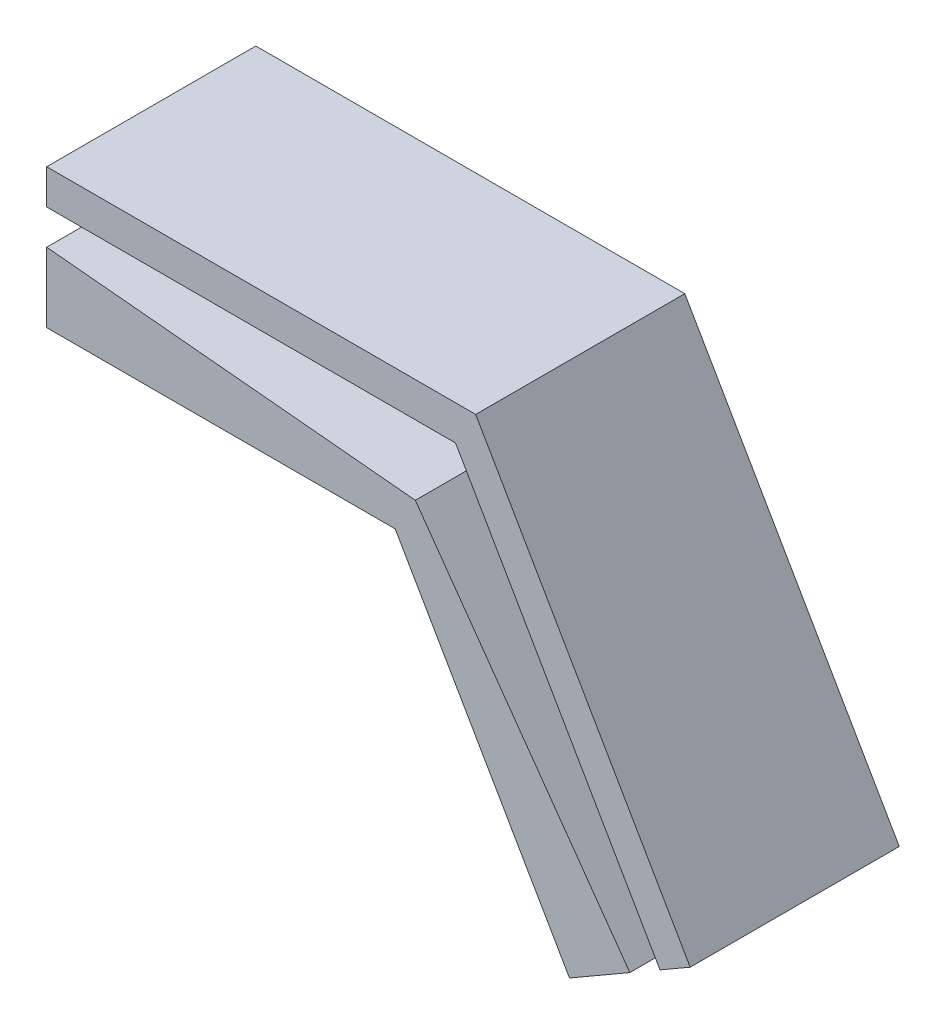
SolidWorks part; units mm, degrees
ref_plane "Alzado" through (0, 0, 0) normal (0, 0, 1) x (1, 0, 0)
ref_plane "Planta" through (0, 0, 0) normal (0, 1, 0) x (1, 0, 0)
ref_plane "Vista lateral" through (0, 0, 0) normal (1, 0, 0) x (0, 0, -1)
sketch "Croquis1" plane through (0, 0, 0) normal (0, 0, 1) x (1, 0, 0)
  line L0 (-111.6684, 35.9239) -> (-101.6684, 35.9239)
  line L1 (-101.6684, 35.9239) -> (-101.6684, 28.4872) construction
  line L2 (-101.6684, 35.9239) -> (-96.6684, 27.2636)
  line L3 (-111.6684, 35.9239) -> (-111.6684, 39.9239)
  line L5 (-96.6684, 27.2636) -> (-93.2043, 29.2636)
  line L6 (-93.2043, 29.2636) -> (-99.359, 39.9239)
  line L7 (-99.359, 39.9239) -> (-111.6684, 39.9239)
  dimension "D1" = 30
extrude "Saliente-Extruir1" add sketch "Croquis1" along normal blind 6
sketch "Croquis2" plane through (0, 0, 6) normal (0, 0, 1) x (1, 0, 0)
  line L0 (-111.6684, 37.9239) -> (-111.6684, 38.9239)
  line L1 (-111.6684, 39.9239) -> (-111.6684, 35.9239) construction
  line L2 (-111.6684, 38.9239) -> (-99.9363, 38.9239)
  line L3 (-94.9363, 28.2636) -> (-94.0703, 28.7636)
  line L4 (-96.6684, 27.2636) -> (-93.2043, 29.2636) construction
  line L5 (-94.0703, 28.7636) -> (-99.9363, 38.9239)
  line L10 (-101.091, 36.9239) -> (-111.6684, 37.9239)
  line L11 (-101.091, 36.9239) -> (-94.9363, 28.2636)
extrude "Cortar-Extruir1" cut sketch "Croquis2" against normal blind 5
